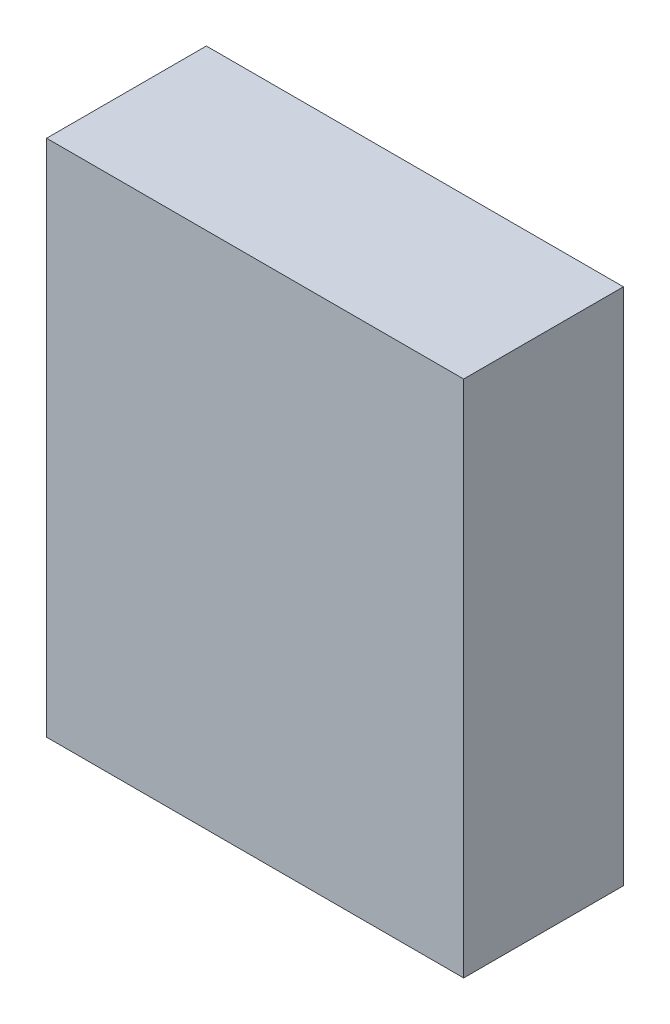
SolidWorks part; units mm, degrees
ref_plane "Front Plane" through (0, 0, 0) normal (0, 0, 1) x (1, 0, 0)
ref_plane "Top Plane" through (0, 0, 0) normal (0, 1, 0) x (1, 0, 0)
ref_plane "Right Plane" through (0, 0, 0) normal (1, 0, 0) x (0, 0, -1)
sketch "Sketch1" plane through (0, 0, 0) normal (0, 0, 1) x (1, 0, 0)
  line L0 (-1.3055, 1.6555) -> (1.3055, 1.6555)
  line L1 (1.3055, 1.6555) -> (1.3055, -1.592)
  line L2 (1.3055, -1.592) -> (-1.3055, -1.592)
  line L3 (-1.3055, -1.592) -> (-1.3055, 1.6555)
extrude "Component_Outline" add sketch "Sketch1" along normal blind 1 separate body
sketch3d "3DSketch1"
  line L0 (0, 0, 0) -> (1, 0, 0)
  line L1 (0, 0, 0) -> (0, 1, 0)
  line L2 (0, 0, 0) -> (0, 0, 1)
  point P0 (0, 0, 0)
